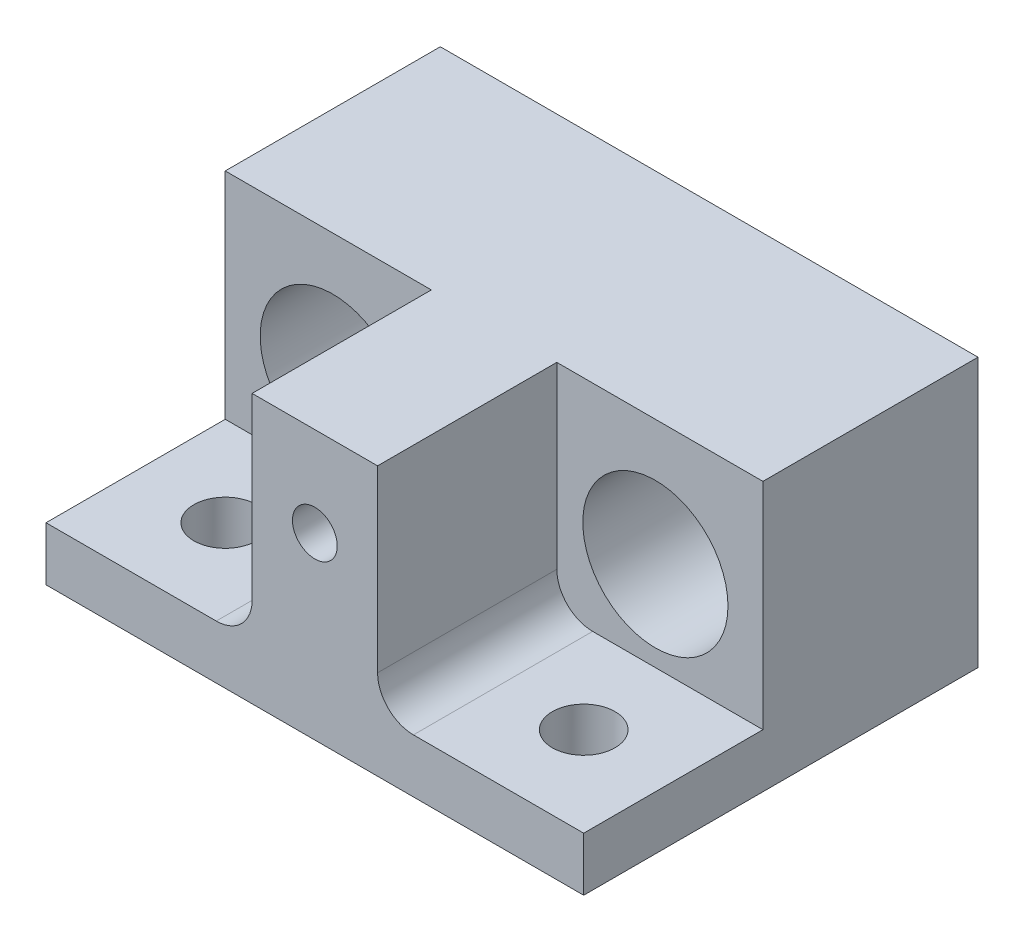
SolidWorks part; units mm, degrees
material "2024-T3"
ref_plane "Plan de face" through (0, 0, 0) normal (0, 0, 1) x (1, 0, 0)
ref_plane "Plan de dessus" through (0, 0, 0) normal (0, 1, 0) x (1, 0, 0)
ref_plane "Plan de droite" through (0, 0, 0) normal (1, 0, 0) x (0, 0, -1)
sketch "Esquisse1" plane through (0, 0, 0) normal (0, 1, 0) x (1, 0, 0)
  line L1 (-15, -11) -> (15, -11)
  line L2 (-15, -11) -> (-15, 11)
  line L3 (-15, 11) -> (15, 11)
  line L4 (15, -11) -> (15, 11)
  line L5 (-15, -11) -> (15, 11) construction
  line L6 (-15, 11) -> (15, -11) construction
  point P0 (0, 0)
  dimension "D1" = 30
  dimension "D2" = 22
extrude "Boss.-Extru.1" add sketch "Esquisse1" along normal blind 15
sketch "Esquisse2" plane through (0, 15, 0) normal (0, 1, 0) x (1, 0, 0)
  line L0 (-15, -11) -> (-3.5, -11)
  line L1 (-15, -11) -> (-15, -1)
  line L2 (-3.5, -11) -> (-3.5, -1)
  line L3 (-15, -1) -> (-3.5, -1)
  line L4 (-15, -11) -> (15, -11) construction
  line L5 (3.5, -11) -> (15, -11)
  line L6 (3.5, -11) -> (3.5, -1)
  line L7 (15, -11) -> (15, -1)
  line L8 (3.5, -1) -> (15, -1)
  dimension "D1" = 10
  dimension "D2" = 11.5
  dimension "D3" = 11.5
  dimension "D4" = 10
extrude "Enlèv. mat.-Extru.2" cut sketch "Esquisse2" against normal blind 12
fillet "Congé1" radius 2 2 edges at (3.5, 3, 6) (-3.5, 3, 6)
sketch "Esquisse3" plane through (0, 0, 1) normal (0, 0, 1) x (1, 0, 0)
  line L2 (-15, 3) -> (-15, 15) construction
  line L3 (-3.5, 15) -> (-15, 15) construction
  line L4 (15, 15) -> (3.5, 15) construction
  circle A0 centre (-9, 8) radius 4.05
  circle A1 centre (9, 8) radius 4.05
  dimension "D2" = 8.1
  dimension "D4" = 8.1
  dimension "D1" = 7
  dimension "D3" = 7
  dimension "D5" = 18
  dimension "D6" = 6
extrude "Enlèv. mat.-Extru.3" cut sketch "Esquisse3" against normal through all
sketch "Esquisse4" plane through (0, 3, 0) normal (0, 1, 0) x (1, 0, 0)
  line L0 (-15, -11) -> (-5.5, -11) construction
  line L1 (5.5, -11) -> (15, -11) construction
  line L2 (-15, -1) -> (-15, -11) construction
  line L3 (15, -11) -> (15, -1) construction
  circle A0 centre (-10, -6) radius 1.75
  circle A1 centre (10, -6) radius 1.75
  dimension "D1" = 3.5
  dimension "D2" = 3.5
  dimension "D3" = 5
  dimension "D4" = 5
  dimension "D5" = 5
  dimension "D6" = 5
extrude "Enlèv. mat.-Extru.4" cut sketch "Esquisse4" against normal up to next
hole_wizard "Trou taraudé M31" positions "Esquisse7" profile "Esquisse6" tap size "M3" standard "ISO"
sketch "Esquisse7" plane through (0, 0, 11) normal (0, 0, 1) x (1, 0, 0)
  point P0 (0, 10)
sketch "Esquisse6" plane through (0, 10, 11) normal (1, 0, 0) x (0, -1, 0)
  line L0 (0, 0) -> (0, 10.7511)
  line L1 (0, 10.7511) -> (1.25, 10)
  line L2 (1.25, 10) -> (1.25, 0)
  line L5 (1.25, 0) -> (0, 0)
  line L10 (0, 10.7511) -> (-1.25, 10) construction
  line L11 (0, -6.35) -> (0, 107.95) construction
  dimension "Diamètre du trou pour taraudage" = 2.5
  dimension "Profondeur du trou pour taraudage" = 10
  dimension "Angle de pointe" = 118
cosmetic thread "Filetage de perçage1" parameters "D1"=8, "D2"=3
